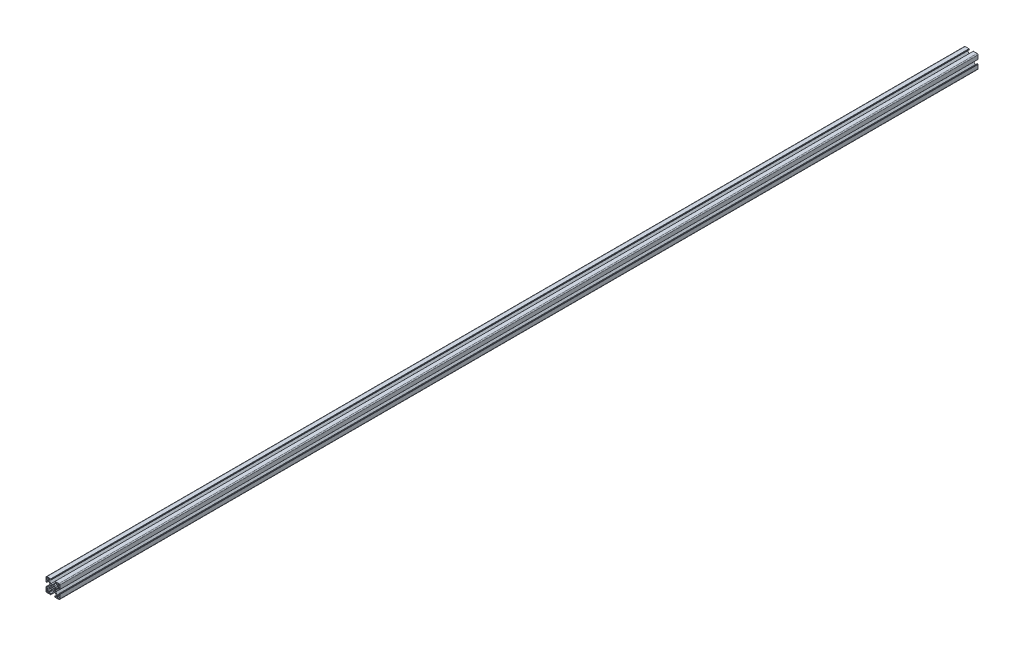
SolidWorks part; units mm, degrees
ref_plane "Płaszczyzna przednia" through (0, 0, 0) normal (0, 0, 1) x (1, 0, 0)
ref_plane "Płaszczyzna górna" through (0, 0, 0) normal (0, 1, 0) x (1, 0, 0)
ref_plane "Płaszczyzna prawa" through (0, 0, 0) normal (1, 0, 0) x (0, 0, -1)
sketch "Sketch1" plane through (0, 0, 0) normal (0, 0, 1) x (1, 0, 0)
  line L0 (109.26, 48.76) -> (107.06, 48.76)
  line L1 (106.06, 47.76) -> (106.06, 45.56)
  line L2 (107.06, 44.56) -> (109.26, 44.56)
  line L3 (110.26, 45.56) -> (110.26, 47.76)
  line L4 (94.9599, 38.3406) -> (93.4241, 39.5784)
  line L5 (92.0547, 38.2147) -> (93.2794, 36.6601)
  line L6 (93.2794, 33.4599) -> (92.0547, 31.9053)
  line L7 (93.4241, 30.5416) -> (94.9599, 31.7794)
  line L8 (98.1601, 31.7794) -> (99.6959, 30.5416)
  line L9 (101.0653, 31.9053) -> (99.8406, 33.4599)
  line L10 (99.8406, 36.6601) -> (101.0653, 38.2147)
  line L11 (99.6959, 39.5784) -> (98.1601, 38.3406)
  line L12 (83.86, 21.36) -> (86.06, 21.36)
  line L13 (87.06, 22.36) -> (87.06, 24.56)
  line L14 (86.06, 25.56) -> (83.86, 25.56)
  line L15 (82.86, 24.56) -> (82.86, 22.36)
  line L16 (110.26, 22.36) -> (110.26, 24.56)
  line L17 (109.26, 25.56) -> (107.06, 25.56)
  line L18 (106.06, 24.56) -> (106.06, 22.36)
  line L19 (86.06, 48.76) -> (83.86, 48.76)
  line L20 (82.86, 47.76) -> (82.86, 45.56)
  line L21 (83.86, 44.56) -> (86.06, 44.56)
  line L22 (87.06, 45.56) -> (87.06, 47.76)
  line L23 (107.06, 21.36) -> (109.26, 21.36)
  line L24 (96.56, 29.5751) -> (97.46, 29.06)
  line L25 (97.46, 29.06) -> (100.7645, 29.06)
  line L26 (100.7645, 29.06) -> (104.81, 25.01)
  line L27 (104.81, 25.01) -> (104.81, 22.46)
  line L28 (104.61, 22.26) -> (101.21, 22.26)
  line L29 (100.61, 21.66) -> (100.61, 20.76)
  line L30 (100.81, 20.56) -> (100.91, 20.56)
  line L31 (101.11, 20.36) -> (101.11, 20.26)
  line L32 (101.31, 20.06) -> (109.56, 20.06)
  line L33 (111.56, 22.06) -> (111.56, 30.31)
  line L34 (111.36, 30.51) -> (111.26, 30.51)
  line L35 (111.06, 30.71) -> (111.06, 30.81)
  line L36 (110.86, 31.01) -> (109.96, 31.01)
  line L37 (109.36, 30.41) -> (109.36, 27.01)
  line L38 (109.16, 26.81) -> (106.61, 26.81)
  line L39 (106.61, 26.81) -> (102.5645, 30.8555)
  line L40 (102.5645, 30.8555) -> (102.5645, 34.16)
  line L41 (102.5645, 34.16) -> (102.0449, 35.06)
  line L42 (102.0449, 35.06) -> (102.5645, 35.96)
  line L43 (102.5645, 35.96) -> (102.5645, 39.2645)
  line L44 (102.5645, 39.2645) -> (106.61, 43.31)
  line L45 (106.61, 43.31) -> (109.16, 43.31)
  line L46 (109.36, 43.11) -> (109.36, 39.71)
  line L47 (109.96, 39.11) -> (110.86, 39.11)
  line L48 (111.06, 39.31) -> (111.06, 39.41)
  line L49 (111.26, 39.61) -> (111.36, 39.61)
  line L50 (111.56, 39.81) -> (111.56, 48.06)
  line L51 (109.56, 50.06) -> (101.31, 50.06)
  line L52 (101.11, 49.86) -> (101.11, 49.76)
  line L53 (100.91, 49.56) -> (100.81, 49.56)
  line L54 (100.61, 49.36) -> (100.61, 48.46)
  line L55 (101.21, 47.86) -> (104.61, 47.86)
  line L56 (104.81, 47.66) -> (104.81, 45.11)
  line L57 (104.81, 45.11) -> (100.7645, 41.06)
  line L58 (100.7645, 41.06) -> (97.46, 41.06)
  line L59 (97.46, 41.06) -> (96.56, 40.5449)
  line L60 (96.56, 40.5449) -> (95.66, 41.06)
  line L61 (95.66, 41.06) -> (92.3555, 41.06)
  line L62 (92.3555, 41.06) -> (88.31, 45.11)
  line L63 (88.31, 45.11) -> (88.31, 47.66)
  line L64 (88.51, 47.86) -> (91.91, 47.86)
  line L65 (92.51, 48.46) -> (92.51, 49.36)
  line L66 (92.31, 49.56) -> (92.21, 49.56)
  line L67 (92.01, 49.76) -> (92.01, 49.86)
  line L68 (91.81, 50.06) -> (83.56, 50.06)
  line L69 (81.56, 48.06) -> (81.56, 39.81)
  line L70 (81.76, 39.61) -> (81.86, 39.61)
  line L71 (82.06, 39.41) -> (82.06, 39.31)
  line L72 (82.26, 39.11) -> (83.16, 39.11)
  line L73 (83.76, 39.71) -> (83.76, 43.11)
  line L74 (83.96, 43.31) -> (86.51, 43.31)
  line L75 (86.51, 43.31) -> (90.5555, 39.2645)
  line L76 (90.5555, 39.2645) -> (90.5555, 35.96)
  line L77 (90.5555, 35.96) -> (91.0751, 35.06)
  line L78 (91.0751, 35.06) -> (90.5555, 34.16)
  line L79 (90.5555, 34.16) -> (90.5555, 30.8555)
  line L80 (90.5555, 30.8555) -> (86.51, 26.81)
  line L81 (86.51, 26.81) -> (83.96, 26.81)
  line L82 (83.76, 27.01) -> (83.76, 30.41)
  line L83 (83.16, 31.01) -> (82.26, 31.01)
  line L84 (82.06, 30.81) -> (82.06, 30.71)
  line L85 (81.86, 30.51) -> (81.76, 30.51)
  line L86 (81.56, 30.31) -> (81.56, 22.06)
  line L87 (83.56, 20.06) -> (91.81, 20.06)
  line L88 (92.01, 20.26) -> (92.01, 20.36)
  line L89 (92.21, 20.56) -> (92.31, 20.56)
  line L90 (92.51, 20.76) -> (92.51, 21.66)
  line L91 (91.91, 22.26) -> (88.51, 22.26)
  line L92 (88.31, 22.46) -> (88.31, 25.01)
  line L93 (88.31, 25.01) -> (92.3555, 29.06)
  line L94 (92.3555, 29.06) -> (95.66, 29.06)
  line L95 (95.66, 29.06) -> (96.56, 29.5751)
  arc A0 (107.06, 48.76) -> (106.06, 47.76) centre (107.06, 47.76) ccw
  arc A1 (106.06, 45.56) -> (107.06, 44.56) centre (107.06, 45.56) ccw
  arc A2 (109.26, 44.56) -> (110.26, 45.56) centre (109.26, 45.56) ccw
  arc A3 (110.26, 47.76) -> (109.26, 48.76) centre (109.26, 47.76) ccw
  arc A4 (93.4241, 39.5784) -> (92.0547, 38.2147) centre (96.56, 35.06) ccw
  arc A5 (93.2794, 36.6601) -> (93.2794, 33.4599) centre (96.56, 35.06) ccw
  arc A6 (92.0547, 31.9053) -> (93.4241, 30.5416) centre (96.56, 35.06) ccw
  arc A7 (94.9599, 31.7794) -> (98.1601, 31.7794) centre (96.56, 35.06) ccw
  arc A8 (99.6959, 30.5416) -> (101.0653, 31.9053) centre (96.56, 35.06) ccw
  arc A9 (99.8406, 33.4599) -> (99.8406, 36.6601) centre (96.56, 35.06) ccw
  arc A10 (101.0653, 38.2147) -> (99.6959, 39.5784) centre (96.56, 35.06) ccw
  arc A11 (98.1601, 38.3406) -> (94.9599, 38.3406) centre (96.56, 35.06) ccw
  arc A12 (86.06, 21.36) -> (87.06, 22.36) centre (86.06, 22.36) ccw
  arc A13 (87.06, 24.56) -> (86.06, 25.56) centre (86.06, 24.56) ccw
  arc A14 (83.86, 25.56) -> (82.86, 24.56) centre (83.86, 24.56) ccw
  arc A15 (82.86, 22.36) -> (83.86, 21.36) centre (83.86, 22.36) ccw
  arc A16 (109.26, 21.36) -> (110.26, 22.36) centre (109.26, 22.36) ccw
  arc A17 (110.26, 24.56) -> (109.26, 25.56) centre (109.26, 24.56) ccw
  arc A18 (107.06, 25.56) -> (106.06, 24.56) centre (107.06, 24.56) ccw
  arc A19 (106.06, 22.36) -> (107.06, 21.36) centre (107.06, 22.36) ccw
  arc A20 (83.86, 48.76) -> (82.86, 47.76) centre (83.86, 47.76) ccw
  arc A21 (82.86, 45.56) -> (83.86, 44.56) centre (83.86, 45.56) ccw
  arc A22 (86.06, 44.56) -> (87.06, 45.56) centre (86.06, 45.56) ccw
  arc A23 (87.06, 47.76) -> (86.06, 48.76) centre (86.06, 47.76) ccw
  arc A24 (104.61, 22.26) -> (104.81, 22.46) centre (104.61, 22.46) ccw
  arc A25 (101.21, 22.26) -> (100.61, 21.66) centre (101.21, 21.66) ccw
  arc A26 (100.61, 20.76) -> (100.81, 20.56) centre (100.81, 20.76) ccw
  arc A27 (101.11, 20.36) -> (100.91, 20.56) centre (100.91, 20.36) ccw
  arc A28 (101.11, 20.26) -> (101.31, 20.06) centre (101.31, 20.26) ccw
  arc A29 (109.56, 20.06) -> (111.56, 22.06) centre (109.56, 22.06) ccw
  arc A30 (111.56, 30.31) -> (111.36, 30.51) centre (111.36, 30.31) ccw
  arc A31 (111.06, 30.71) -> (111.26, 30.51) centre (111.26, 30.71) ccw
  arc A32 (111.06, 30.81) -> (110.86, 31.01) centre (110.86, 30.81) ccw
  arc A33 (109.96, 31.01) -> (109.36, 30.41) centre (109.96, 30.41) ccw
  arc A34 (109.16, 26.81) -> (109.36, 27.01) centre (109.16, 27.01) ccw
  arc A35 (109.36, 43.11) -> (109.16, 43.31) centre (109.16, 43.11) ccw
  arc A36 (109.36, 39.71) -> (109.96, 39.11) centre (109.96, 39.71) ccw
  arc A37 (110.86, 39.11) -> (111.06, 39.31) centre (110.86, 39.31) ccw
  arc A38 (111.26, 39.61) -> (111.06, 39.41) centre (111.26, 39.41) ccw
  arc A39 (111.36, 39.61) -> (111.56, 39.81) centre (111.36, 39.81) ccw
  arc A40 (111.56, 48.06) -> (109.56, 50.06) centre (109.56, 48.06) ccw
  arc A41 (101.31, 50.06) -> (101.11, 49.86) centre (101.31, 49.86) ccw
  arc A42 (100.91, 49.56) -> (101.11, 49.76) centre (100.91, 49.76) ccw
  arc A43 (100.81, 49.56) -> (100.61, 49.36) centre (100.81, 49.36) ccw
  arc A44 (100.61, 48.46) -> (101.21, 47.86) centre (101.21, 48.46) ccw
  arc A45 (104.81, 47.66) -> (104.61, 47.86) centre (104.61, 47.66) ccw
  arc A46 (88.51, 47.86) -> (88.31, 47.66) centre (88.51, 47.66) ccw
  arc A47 (91.91, 47.86) -> (92.51, 48.46) centre (91.91, 48.46) ccw
  arc A48 (92.51, 49.36) -> (92.31, 49.56) centre (92.31, 49.36) ccw
  arc A49 (92.01, 49.76) -> (92.21, 49.56) centre (92.21, 49.76) ccw
  arc A50 (92.01, 49.86) -> (91.81, 50.06) centre (91.81, 49.86) ccw
  arc A51 (83.56, 50.06) -> (81.56, 48.06) centre (83.56, 48.06) ccw
  arc A52 (81.56, 39.81) -> (81.76, 39.61) centre (81.76, 39.81) ccw
  arc A53 (82.06, 39.41) -> (81.86, 39.61) centre (81.86, 39.41) ccw
  arc A54 (82.06, 39.31) -> (82.26, 39.11) centre (82.26, 39.31) ccw
  arc A55 (83.16, 39.11) -> (83.76, 39.71) centre (83.16, 39.71) ccw
  arc A56 (83.96, 43.31) -> (83.76, 43.11) centre (83.96, 43.11) ccw
  arc A57 (83.76, 27.01) -> (83.96, 26.81) centre (83.96, 27.01) ccw
  arc A58 (83.76, 30.41) -> (83.16, 31.01) centre (83.16, 30.41) ccw
  arc A59 (82.26, 31.01) -> (82.06, 30.81) centre (82.26, 30.81) ccw
  arc A60 (81.86, 30.51) -> (82.06, 30.71) centre (81.86, 30.71) ccw
  arc A61 (81.76, 30.51) -> (81.56, 30.31) centre (81.76, 30.31) ccw
  arc A62 (81.56, 22.06) -> (83.56, 20.06) centre (83.56, 22.06) ccw
  arc A63 (91.81, 20.06) -> (92.01, 20.26) centre (91.81, 20.26) ccw
  arc A64 (92.21, 20.56) -> (92.01, 20.36) centre (92.21, 20.36) ccw
  arc A65 (92.31, 20.56) -> (92.51, 20.76) centre (92.31, 20.76) ccw
  arc A66 (92.51, 21.66) -> (91.91, 22.26) centre (91.91, 21.66) ccw
  arc A67 (88.31, 22.46) -> (88.51, 22.26) centre (88.51, 22.46) ccw
  dimension "D1" = 3.65
  dimension "D2" = 30
  dimension "D3" = 30
  dimension "D4" = 8.1
extrude "Sigma Profile" add sketch "Sketch1" along normal blind 2000
